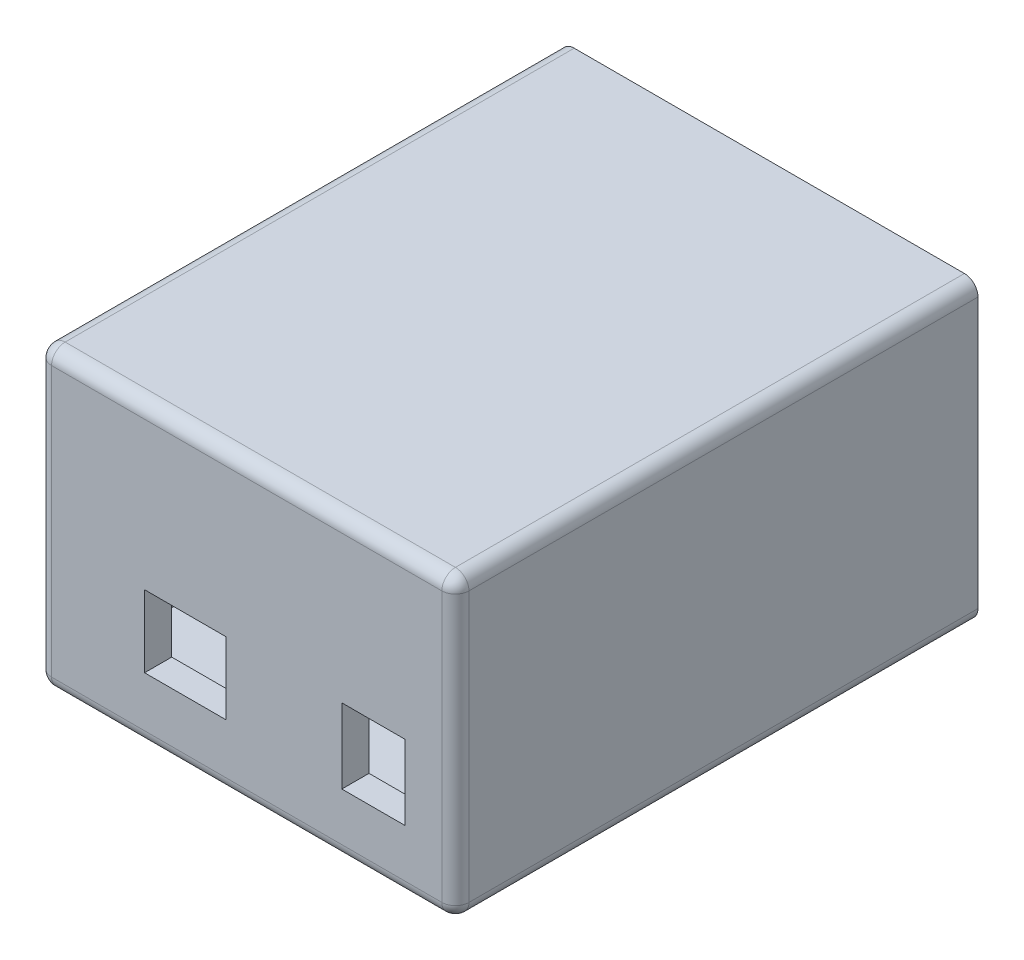
SolidWorks part; units mm, degrees
ref_plane "Plan de face" through (0, 0, 0) normal (0, 0, 1) x (1, 0, 0)
ref_plane "Plan de dessus" through (0, 0, 0) normal (0, 1, 0) x (1, 0, 0)
ref_plane "Plan de droite" through (0, 0, 0) normal (1, 0, 0) x (0, 0, -1)
sketch "Esquisse1" plane through (0, 0, 0) normal (0, 0, 1) x (1, 0, 0)
  line L1 (-31.6005, 34.6263) -> (29.8995, 34.6263)
  line L2 (-31.6005, 34.6263) -> (-31.6005, -9.1237)
  line L3 (-31.6005, -9.1237) -> (29.8995, -9.1237)
  line L4 (29.8995, 34.6263) -> (29.8995, -9.1237)
  dimension "D1" = 43.75
  dimension "D2" = 61.5
extrude "Boss.-Extru.1" add sketch "Esquisse1" along normal blind 77
sketch "Esquisse2" plane through (0, 34.6263, 0) normal (0, 1, 0) x (1, 0, 0)
  line L0 (29.8995, -77) -> (-31.6005, -77) construction
  line L1 (25.8995, -4) -> (-27.6005, -4)
  line L2 (25.8995, -4) -> (25.8995, -73)
  line L3 (25.8995, -73) -> (-27.6005, -73)
  line L4 (-27.6005, -4) -> (-27.6005, -73)
  line L5 (29.8995, -77) -> (29.8995, 0) construction
  dimension "D1" = 69
  dimension "D2" = 53.5
  dimension "D3" = 4
  dimension "D4" = 4
sketch "Esquisse3" plane through (0, 0, 77) normal (0, 0, 1) x (1, 0, 0)
  line L0 (-31.6005, -9.1237) -> (29.8995, -9.1237) construction
  line L1 (-27.6005, -5.1237) -> (25.8995, -5.1237)
  line L2 (-27.6005, -5.1237) -> (-27.6005, 30.6263)
  line L3 (-27.6005, 30.6263) -> (25.8995, 30.6263)
  line L4 (25.8995, -5.1237) -> (25.8995, 30.6263)
  line L5 (29.8995, -9.1237) -> (29.8995, 34.6263) construction
  line L7 (13.1695, 10.9763) -> (22.4695, 10.9763)
  line L8 (13.1695, 10.9763) -> (13.1695, -0.0237)
  line L9 (13.1695, -0.0237) -> (22.4695, -0.0237)
  line L10 (22.4695, 10.9763) -> (22.4695, -0.0237)
  line L11 (-15.9005, 10.8763) -> (-3.9005, 10.8763)
  line L12 (-15.9005, 10.8763) -> (-15.9005, 0.2763)
  line L13 (-15.9005, 0.2763) -> (-3.9005, 0.2763)
  line L14 (-3.9005, 10.8763) -> (-3.9005, 0.2763)
  point P16 (0, 0)
  point P17 (0, 0)
  point P18 (0, 0)
  point P19 (0, 0)
  point P20 (0, 0)
  point P21 (0, 0)
  dimension "D1" = 53.5
  dimension "D2" = 35.75
  dimension "D3" = 4
  dimension "D4" = 4
  dimension "D5" = 11
  dimension "D6" = 9.3
  dimension "D7" = 12
  dimension "D8" = 10.6
  dimension "D9" = 11.7
  dimension "D10" = 17.07
  dimension "D11" = 5.4
  dimension "D12" = 5.1
extrude "Enlèv. mat.-Extru.4" cut sketch "Esquisse3" against normal up to next contours L14 L13 L12 L11 | L7 L10 L9 L8
sketch "Esquisse6" plane through (0, 0, 0) normal (0, 0, -1) x (-1, 0, 0)
  line L0 (31.6005, -9.1237) -> (-29.8995, -9.1237) construction
  line L1 (-25.8995, 30.6263) -> (27.6005, 30.6263)
  line L2 (-25.8995, 30.6263) -> (-25.8995, -5.1237)
  line L3 (-25.8995, -5.1237) -> (27.6005, -5.1237)
  line L4 (27.6005, 30.6263) -> (27.6005, -5.1237)
  line L5 (31.6005, 34.6263) -> (31.6005, -9.1237) construction
  dimension "D1" = 53.5
  dimension "D2" = 35.75
  dimension "D3" = 4
  dimension "D4" = 4
extrude "Enlèv. mat.-Extru.5" cut sketch "Esquisse6" against normal blind 73
fillet "Congé4" radius 2 8 edges at (-31.6005, 34.6263, 38.5) (-31.6005, -9.1237, 38.5) (-31.6005, 12.7513, 77) (-0.8505, -9.1237, 77) (29.8995, -9.1237, 38.5) (29.8995, 12.7513, 77) (-0.8505, 34.6263, 77) (29.8995, 34.6263, 38.5)
